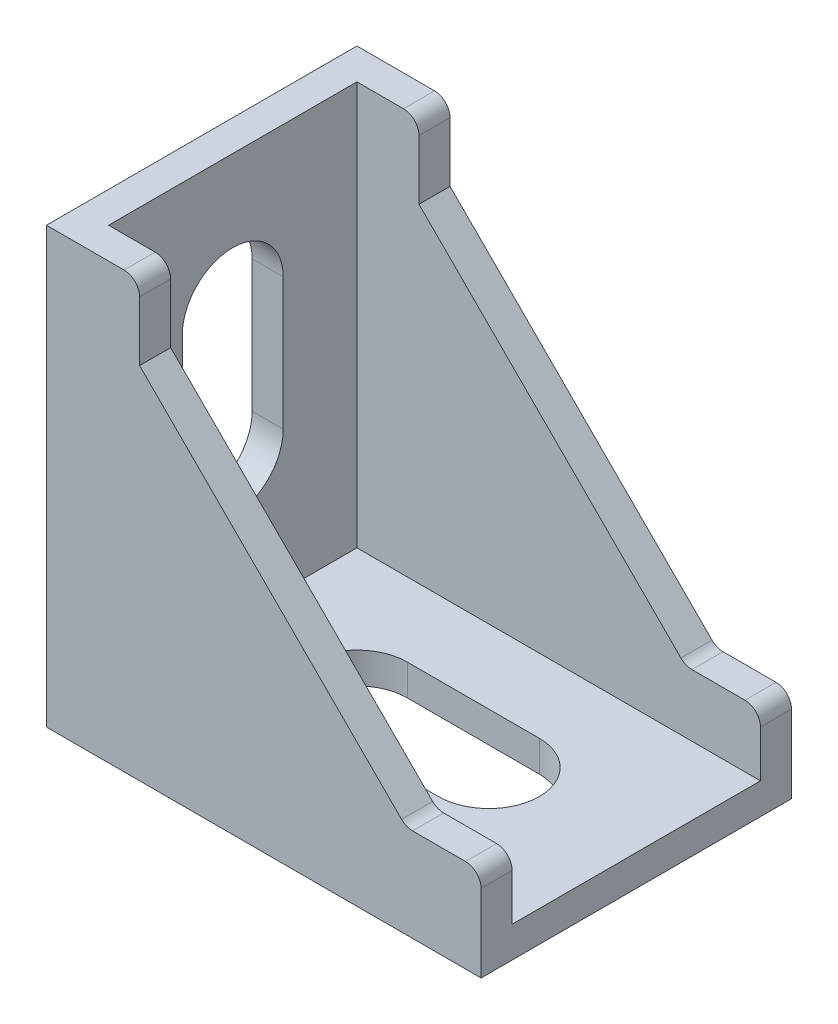
SolidWorks part; units mm, degrees
ref_plane "Front" through (0, 0, 0) normal (0, 0, 1) x (1, 0, 0)
ref_plane "Top" through (0, 0, 0) normal (0, 1, 0) x (1, 0, 0)
ref_plane "Right" through (0, 0, 0) normal (1, 0, 0) x (0, 0, -1)
sketch "草图1" plane through (0, 0, 0) normal (0, 0, 1) x (1, 0, 0)
  line L0 (0, 0) -> (0, 28)
  line L1 (0, 28) -> (6, 28)
  line L2 (6, 28) -> (6, 23.169)
  line L3 (6, 23.169) -> (23.169, 6)
  line L4 (23.169, 6) -> (28, 6)
  line L5 (28, 6) -> (28, 0)
  line L6 (28, 0) -> (0, 0)
  dimension "D1" = 28
  dimension "D2" = 28
  dimension "D3" = 6
  dimension "D4" = 6
  dimension "D5" = 135
extrude "凸台-拉伸1" add sketch "草图1" along normal blind 20
sketch "草图2" plane through (28, 0, 0) normal (1, 0, 0) x (0, 0, -1)
  line L1 (-2, 28) -> (-18, 28)
  line L2 (-2, 28) -> (-2, 2)
  line L3 (-2, 2) -> (-18, 2)
  line L4 (-18, 28) -> (-18, 2)
  line L5 (-2, 28) -> (-18, 2) construction
  line L6 (-2, 2) -> (-18, 28) construction
  line L7 (-20, 0) -> (0, 0) construction
  line L8 (-20, 6) -> (-20, 23.169) construction
  line L9 (0, 6) -> (0, 23.169) construction
  line L10 (-20, 28) -> (0, 28) construction
  point P0 (-10, 15)
  dimension "D2" = 2
  dimension "D3" = 2
  dimension "D4" = 2
extrude "切除-拉伸1" cut sketch "草图2" against normal offset from surface (26 mm away) 2 up to face at (0, 14, 10)
sketch "草图3" plane through (2, 0, 0) normal (1, 0, 0) x (0, 0, -1)
  line L0 (-10, 11) -> (-10, 19.5) construction
  line L1 (-13.25, 11) -> (-13.25, 19.5)
  line L2 (-6.75, 11) -> (-6.75, 19.5)
  line L3 (-10, 11) -> (-10, 2) construction
  line L4 (-2, 2) -> (-18, 2) construction
  arc A0 (-13.25, 11) -> (-6.75, 11) centre (-10, 11) ccw
  arc A1 (-6.75, 19.5) -> (-13.25, 19.5) centre (-10, 19.5) ccw
  point P2 (-10, 15.25)
  dimension "D1" = 6.5
  dimension "D2" = 8.5
  dimension "D3" = 9
sketch "草图4" plane through (0, 2, 2) normal (0, 1, 0) x (1, 0, 0)
  line L0 (10, -8) -> (18.5, -8) construction
  line L1 (10, -4.75) -> (18.5, -4.75)
  line L2 (10, -11.25) -> (18.5, -11.25)
  line L6 (10, -8) -> (2, -8) construction
  arc A0 (10, -4.75) -> (10, -11.25) centre (10, -8) ccw
  arc A1 (18.5, -11.25) -> (18.5, -4.75) centre (18.5, -8) ccw
  point P2 (14.25, -8)
  dimension "D3" = 8
  dimension "D1" = 6.5
  dimension "D2" = 8.5
extrude "切除-拉伸2" cut sketch "草图3" against normal up to next
extrude "切除-拉伸3" cut sketch "草图4" against normal up to next
fillet "圆角1" radius 1 6 edges at (28, 6, 1) (28, 6, 19) (23.169, 6, 1) (23.169, 6, 19) (6, 28, 1) (6, 28, 19)
